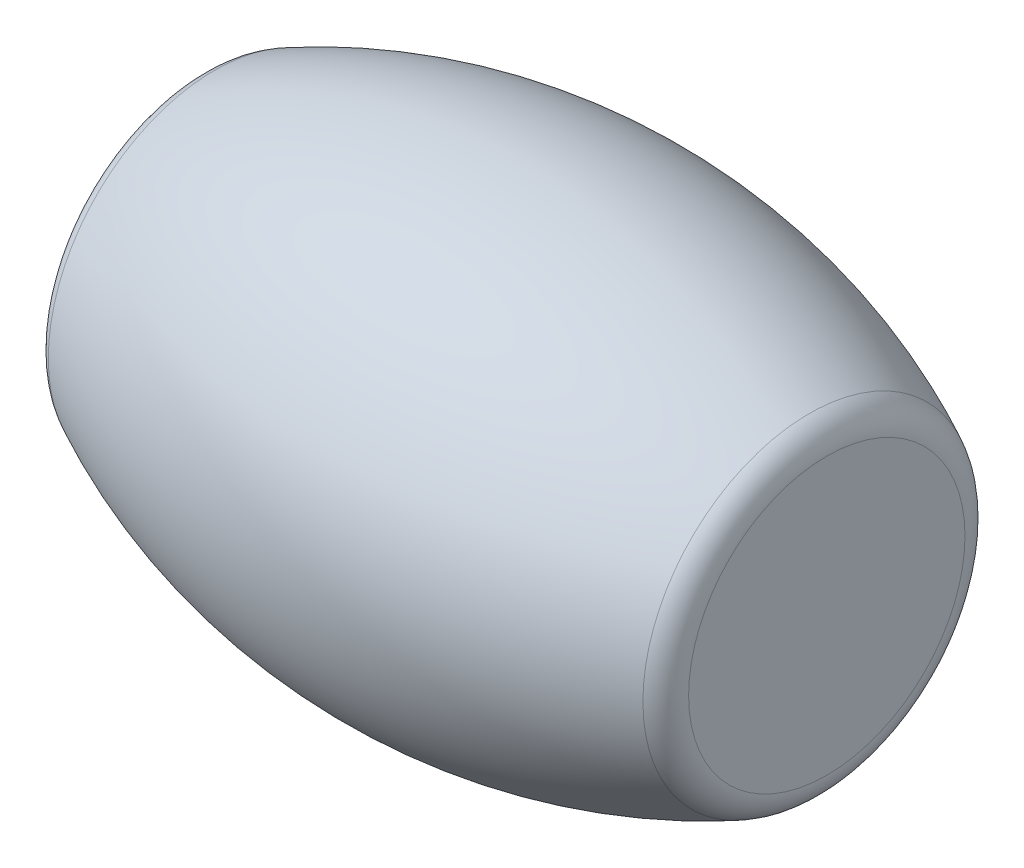
SolidWorks part; units mm, degrees
ref_plane "Front Plane" through (0, 0, 0) normal (0, 0, 1) x (1, 0, 0)
ref_plane "Top Plane" through (0, 0, 0) normal (0, 1, 0) x (1, 0, 0)
ref_plane "Right Plane" through (0, 0, 0) normal (1, 0, 0) x (0, 0, -1)
other "Center of Mass"
sketch "Sketch1" plane through (0, 0, 0) normal (0, 0, 1) x (1, 0, 0)
  line L0 (0, 0) -> (25.4, 0)
  line L1 (25.4, 0) -> (25.4, 12.7)
  line L2 (0, 0) -> (0, 19.05)
  line L3 (0, 19.05) -> (25.4, 19.05) construction
  arc A0 (0, 19.05) -> (25.4, 12.7) centre (0, -34.925) cw
  point P6 (0, 0)
  dimension "D1" = 12.7
  dimension "D2" = 19.05
  dimension "D3" = 25.4
revolve "Revolve2" add sketch "Sketch1" angle 360 about L0
fillet "Fillet1" radius 2.54 1 edges at (25.4, 0, 12.7)
mirror "Mirror2" about plane through (0, 0, 0) normal (-1, 0, 0) of "Revolve2", "Fillet1"
sketch3d "URDF Reference"
  line L0 (0, 0, 0) -> (10, 0, 0) construction
  line L1 (0, 0, 0) -> (0, 0, -10) construction
  point P0 (0, 0, 0)
  point P1 (0, 0, 0)
